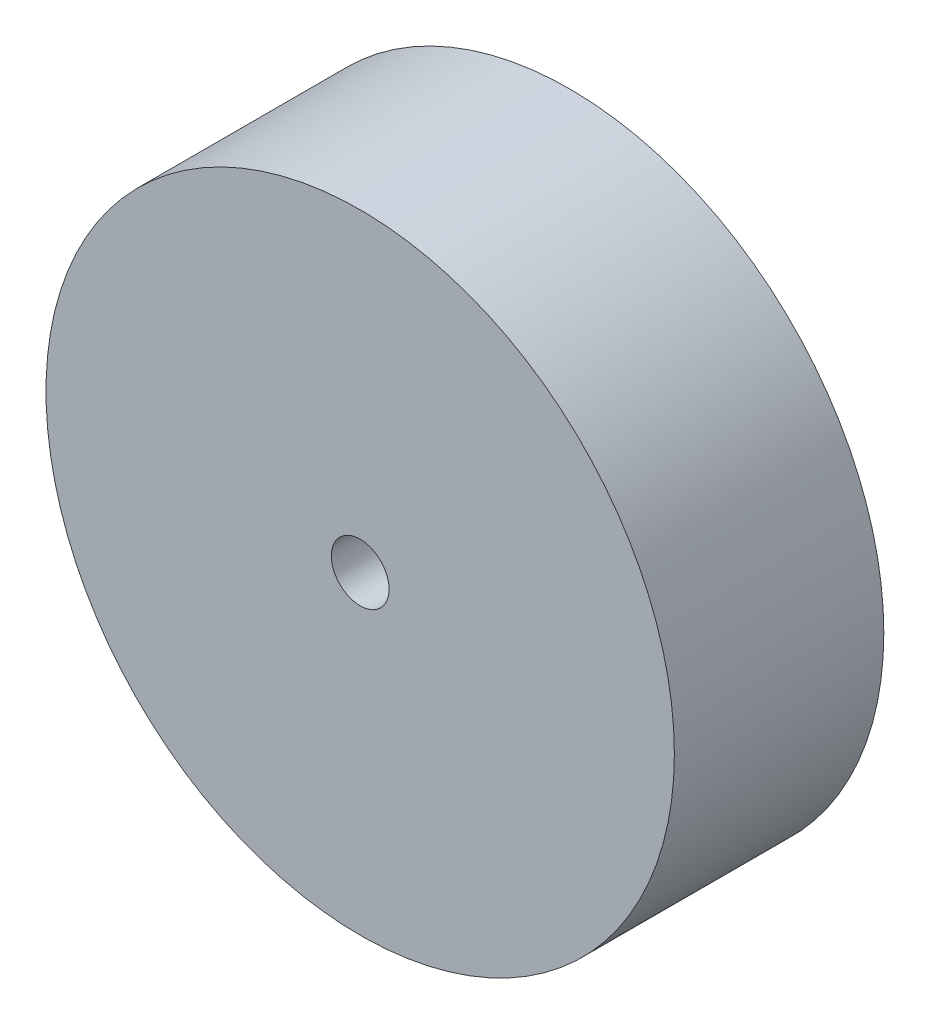
SolidWorks part; units mm, degrees
ref_plane "Plan de face" through (0, 0, 0) normal (0, 0, 1) x (1, 0, 0)
ref_plane "Plan de dessus" through (0, 0, 0) normal (0, 1, 0) x (1, 0, 0)
ref_plane "Plan de droite" through (0, 0, 0) normal (1, 0, 0) x (0, 0, -1)
sketch "Esquisse1" plane through (0, 0, 0) normal (0, 0, 1) x (1, 0, 0)
  circle A0 centre (0, 0) radius 19.05
  circle A1 centre (0, 0) radius 1.75
  dimension "D1" = 38.1
  dimension "D2" = 3.5
extrude "Boss.-Extru.1" add sketch "Esquisse1" along normal blind 12.7
